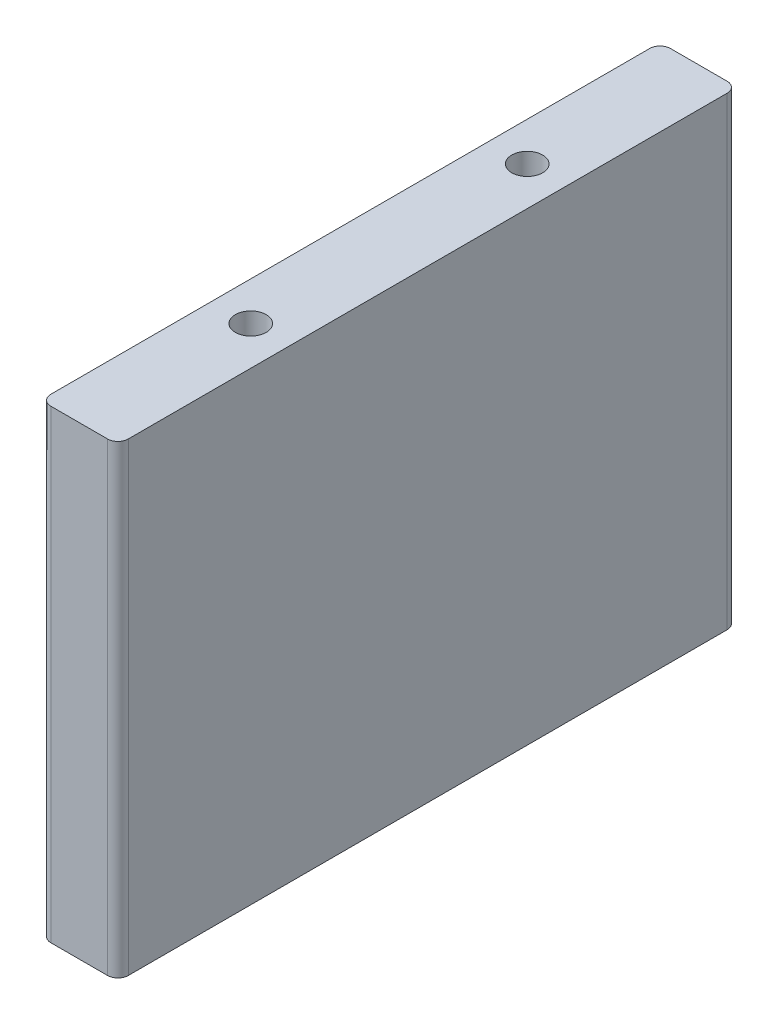
SolidWorks part; units mm, degrees
ref_plane "Front Plane" through (0, 0, 0) normal (0, 0, 1) x (1, 0, 0)
ref_plane "Top Plane" through (0, 0, 0) normal (0, 1, 0) x (1, 0, 0)
ref_plane "Right Plane" through (0, 0, 0) normal (1, 0, 0) x (0, 0, -1)
sketch "Sketch1" plane through (0, 0, 0) normal (0, 1, 0) x (1, 0, 0)
  line L1 (-4.7625, 38.1) -> (4.7625, 38.1)
  line L2 (-4.7625, 38.1) -> (-4.7625, -38.1)
  line L3 (-4.7625, -38.1) -> (4.7625, -38.1)
  line L4 (4.7625, 38.1) -> (4.7625, -38.1)
  point P4 (0, 38.1)
  point P6 (4.7625, 0)
  dimension "D1" = 9.525
  dimension "D2" = 76.2
extrude "Boss-Extrude1" add sketch "Sketch1" along normal mid plane 57.15
hole_wizard "#10-24 Tapped Hole1" positions "Sketch2" profile "Sketch3" tap size "#10-24" standard "ANSI Inch"
sketch "Sketch2" plane through (0, 28.575, 0) normal (0, 1, 0) x (1, 0, 0)
  point P0 (0, 17)
  point P2 (0, -17)
  dimension "D1" = 34
  dimension "D2" = 17
sketch "Sketch3" plane through (0, 28.575, -17) normal (1, 0, 0) x (0, 0, 1)
  line L0 (0, 0) -> (0, 20.1908)
  line L1 (0, 20.1908) -> (1.8986, 19.05)
  line L2 (1.8986, 19.05) -> (1.8986, 0)
  line L5 (1.8986, 0) -> (0, 0)
  line L10 (0, 20.1908) -> (-1.8987, 19.05) construction
  line L11 (0, -6.35) -> (0, 107.95) construction
  dimension "Tap Drill Dia." = 3.7973
  dimension "Tap Drill Depth" = 19.05
  dimension "Drill Angle" = 118
cosmetic thread "Hole Thread1" parameters "D1"=15.875, "D2"=4.826
cosmetic thread "Hole Thread2" parameters "D1"=15.875, "D2"=4.826
mirror "Mirror1" about plane through (0, 0, 0) normal (0, 1, 0) of "#10-24 Tapped Hole1"
cosmetic thread "Hole Thread3" parameters "D1"=15.875, "D2"=4.826
cosmetic thread "Hole Thread4" parameters "D1"=15.875, "D2"=4.826
fillet "Fillet1" radius 1.27 4 edges at (4.7625, 0, -38.1) (-4.7625, 0, -38.1) (4.7625, 0, 38.1) (-4.7625, 0, 38.1)
equation "\"D2@Sketch2\"=\"D1@Sketch2\"/2"
